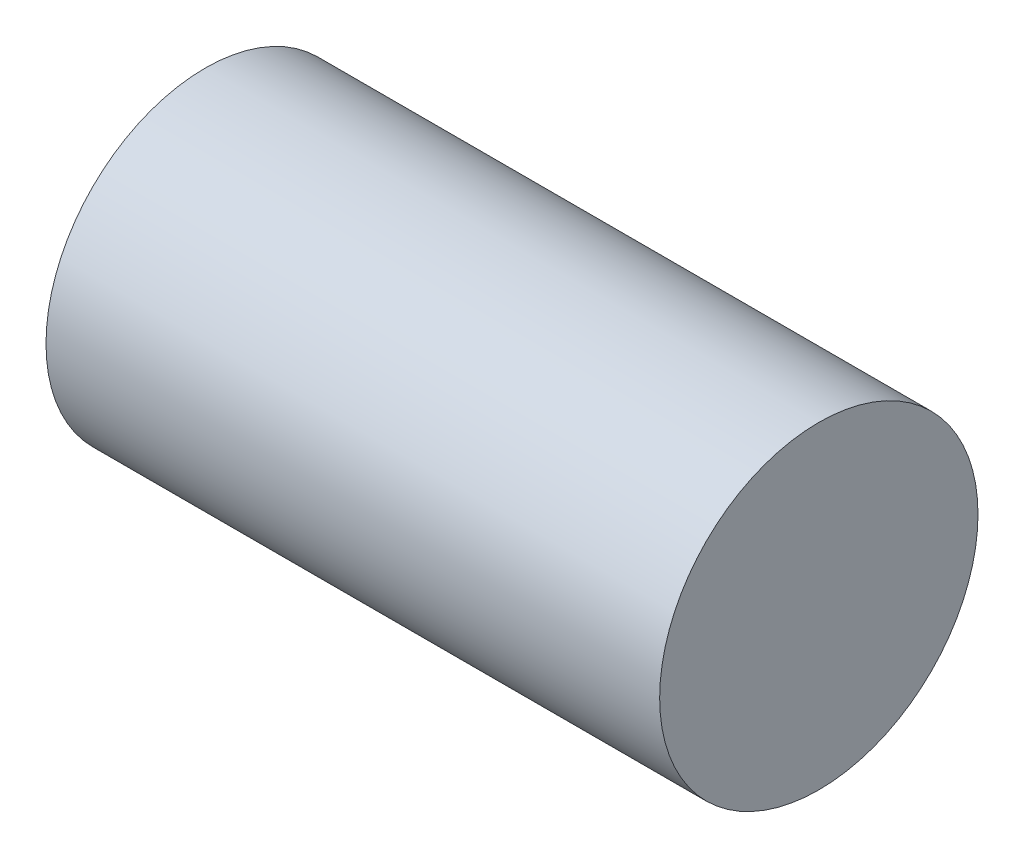
SolidWorks part; units mm, degrees
ref_plane "Front Plane" through (0, 0, 0) normal (0, 0, 1) x (1, 0, 0)
ref_plane "Top Plane" through (0, 0, 0) normal (0, 1, 0) x (1, 0, 0)
ref_plane "Right Plane" through (0, 0, 0) normal (1, 0, 0) x (0, 0, -1)
sketch "Sketch1" plane through (0, 0, 0) normal (1, 0, 0) x (0, 0, -1)
  circle A0 centre (0, 0) radius 12.45
  dimension "D1" = 24.9
extrude "Boss-Extrude1" add sketch "Sketch1" along normal mid plane 48
